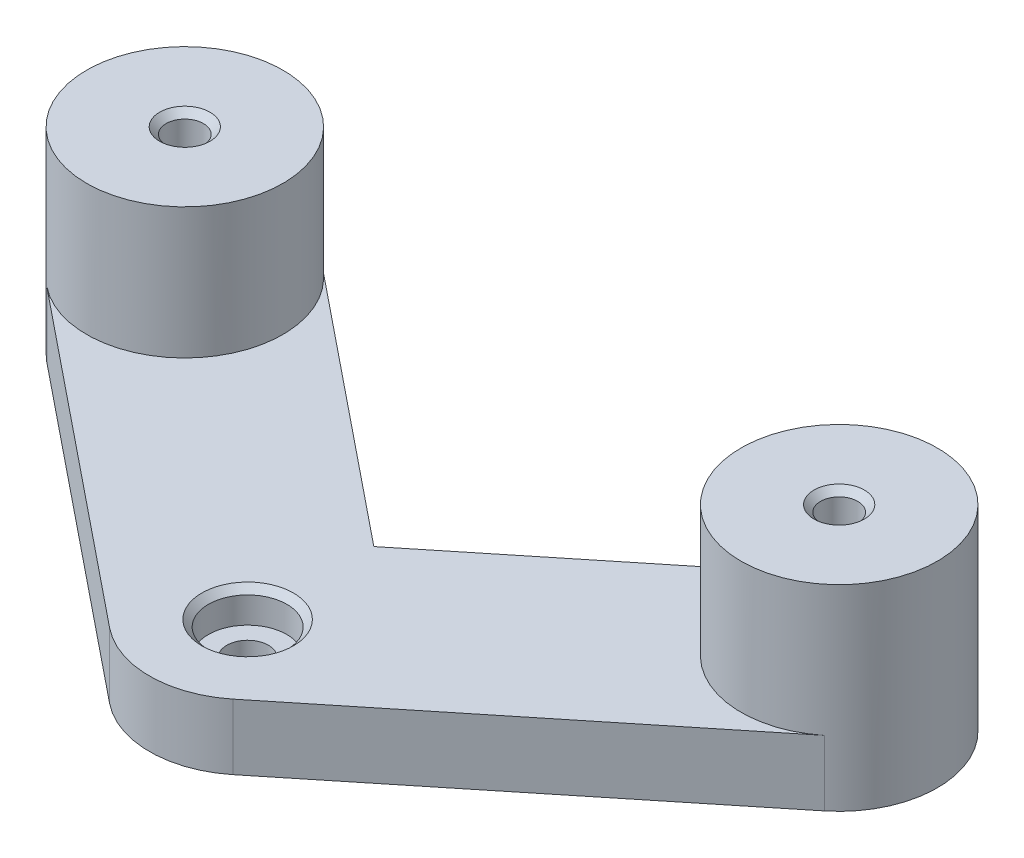
SolidWorks part; units mm, degrees
ref_plane "Front Plane" through (0, 0, 0) normal (0, 0, 1) x (1, 0, 0)
ref_plane "Top Plane" through (0, 0, 0) normal (0, 1, 0) x (1, 0, 0)
ref_plane "Right Plane" through (0, 0, 0) normal (1, 0, 0) x (0, 0, -1)
sketch "Sketch1" plane through (0, 0, 0) normal (0, 1, 0) x (1, 0, 0)
  circle A0 centre (0, 0) radius 100 construction
  circle A1 centre (-100, 0) radius 2.85
  circle A2 centre (-50, 86.6025) radius 2.85
  circle A3 centre (50, 86.6025) radius 2.85
  circle A4 centre (100, 0) radius 2.85
  circle A5 centre (50, -86.6025) radius 2.85
  circle A6 centre (-50, -86.6025) radius 2.85
  point P18 (0, 0)
  dimension "D1" = 200
  dimension "D2" = 5.7
  dimension "D3" = 6
sketch "Sketch3" plane through (0, 0, 0) normal (0, 1, 0) x (1, 0, 0)
  line L0 (-203.2, 152.4) -> (-203.2, -49.2102) construction
  line L1 (-203.2, 152.4) -> (37.0656, 152.4) construction
  circle A0 centre (-203.2, 152.4) radius 3.175
  circle A1 centre (-177.8, 152.4) radius 3.175
  circle A2 centre (-152.4, 152.4) radius 3.175
  circle A3 centre (-127, 152.4) radius 3.175
  circle A4 centre (-101.6, 152.4) radius 3.175
  circle A5 centre (-76.2, 152.4) radius 3.175
  circle A6 centre (-50.8, 152.4) radius 3.175
  circle A7 centre (-25.4, 152.4) radius 3.175
  circle A8 centre (0, 152.4) radius 3.175
  circle A9 centre (25.4, 152.4) radius 3.175
  circle A10 centre (50.8, 152.4) radius 3.175
  circle A11 centre (76.2, 152.4) radius 3.175
  circle A12 centre (101.6, 152.4) radius 3.175
  circle A13 centre (127, 152.4) radius 3.175
  circle A14 centre (152.4, 152.4) radius 3.175
  circle A15 centre (-177.8, 127) radius 3.175
  circle A16 centre (-152.4, 127) radius 3.175
  circle A17 centre (-127, 127) radius 3.175
  circle A18 centre (-101.6, 127) radius 3.175
  circle A19 centre (-76.2, 127) radius 3.175
  circle A20 centre (-50.8, 127) radius 3.175
  circle A21 centre (-25.4, 127) radius 3.175
  circle A22 centre (0, 127) radius 3.175
  circle A23 centre (25.4, 127) radius 3.175
  circle A24 centre (50.8, 127) radius 3.175
  circle A25 centre (76.2, 127) radius 3.175
  circle A26 centre (101.6, 127) radius 3.175
  circle A27 centre (127, 127) radius 3.175
  circle A28 centre (152.4, 127) radius 3.175
  circle A29 centre (-177.8, 101.6) radius 3.175
  circle A30 centre (-152.4, 101.6) radius 3.175
  circle A31 centre (-127, 101.6) radius 3.175
  circle A32 centre (-101.6, 101.6) radius 3.175
  circle A33 centre (-76.2, 101.6) radius 3.175
  circle A34 centre (-50.8, 101.6) radius 3.175
  circle A35 centre (-25.4, 101.6) radius 3.175
  circle A36 centre (0, 101.6) radius 3.175
  circle A37 centre (25.4, 101.6) radius 3.175
  circle A38 centre (50.8, 101.6) radius 3.175
  circle A39 centre (76.2, 101.6) radius 3.175
  circle A40 centre (101.6, 101.6) radius 3.175
  circle A41 centre (127, 101.6) radius 3.175
  circle A42 centre (152.4, 101.6) radius 3.175
  circle A43 centre (-177.8, 76.2) radius 3.175
  circle A44 centre (-152.4, 76.2) radius 3.175
  circle A45 centre (-127, 76.2) radius 3.175
  circle A46 centre (-101.6, 76.2) radius 3.175
  circle A47 centre (-76.2, 76.2) radius 3.175
  circle A48 centre (-50.8, 76.2) radius 3.175
  circle A49 centre (-25.4, 76.2) radius 3.175
  circle A50 centre (0, 76.2) radius 3.175
  circle A51 centre (25.4, 76.2) radius 3.175
  circle A52 centre (50.8, 76.2) radius 3.175
  circle A53 centre (76.2, 76.2) radius 3.175
  circle A54 centre (101.6, 76.2) radius 3.175
  circle A55 centre (127, 76.2) radius 3.175
  circle A56 centre (152.4, 76.2) radius 3.175
  circle A57 centre (-177.8, 50.8) radius 3.175
  circle A58 centre (-152.4, 50.8) radius 3.175
  circle A59 centre (-127, 50.8) radius 3.175
  circle A60 centre (-101.6, 50.8) radius 3.175
  circle A61 centre (-76.2, 50.8) radius 3.175
  circle A62 centre (-50.8, 50.8) radius 3.175
  circle A63 centre (-25.4, 50.8) radius 3.175
  circle A64 centre (0, 50.8) radius 3.175
  circle A65 centre (25.4, 50.8) radius 3.175
  circle A66 centre (50.8, 50.8) radius 3.175
  circle A67 centre (76.2, 50.8) radius 3.175
  circle A68 centre (101.6, 50.8) radius 3.175
  circle A69 centre (127, 50.8) radius 3.175
  circle A70 centre (152.4, 50.8) radius 3.175
  circle A71 centre (-177.8, 25.4) radius 3.175
  circle A72 centre (-152.4, 25.4) radius 3.175
  circle A73 centre (-127, 25.4) radius 3.175
  circle A74 centre (-101.6, 25.4) radius 3.175
  circle A75 centre (-76.2, 25.4) radius 3.175
  circle A76 centre (-50.8, 25.4) radius 3.175
  circle A77 centre (-25.4, 25.4) radius 3.175
  circle A78 centre (0, 25.4) radius 3.175
  circle A79 centre (25.4, 25.4) radius 3.175
  circle A80 centre (50.8, 25.4) radius 3.175
  circle A81 centre (76.2, 25.4) radius 3.175
  circle A82 centre (101.6, 25.4) radius 3.175
  circle A83 centre (127, 25.4) radius 3.175
  circle A84 centre (152.4, 25.4) radius 3.175
  circle A85 centre (-177.8, 0) radius 3.175
  circle A86 centre (-152.4, 0) radius 3.175
  circle A87 centre (-127, 0) radius 3.175
  circle A88 centre (-101.6, 0) radius 3.175
  circle A89 centre (-76.2, 0) radius 3.175
  circle A90 centre (-50.8, 0) radius 3.175
  circle A91 centre (-25.4, 0) radius 3.175
  circle A92 centre (0, 0) radius 3.175
  circle A93 centre (25.4, 0) radius 3.175
  circle A94 centre (50.8, 0) radius 3.175
  circle A95 centre (76.2, 0) radius 3.175
  circle A96 centre (101.6, 0) radius 3.175
  circle A97 centre (127, 0) radius 3.175
  circle A98 centre (152.4, 0) radius 3.175
  circle A99 centre (-177.8, -25.4) radius 3.175
  circle A100 centre (-152.4, -25.4) radius 3.175
  circle A101 centre (-127, -25.4) radius 3.175
  circle A102 centre (-101.6, -25.4) radius 3.175
  circle A103 centre (-76.2, -25.4) radius 3.175
  circle A104 centre (-50.8, -25.4) radius 3.175
  circle A105 centre (-25.4, -25.4) radius 3.175
  circle A106 centre (0, -25.4) radius 3.175
  circle A107 centre (25.4, -25.4) radius 3.175
  circle A108 centre (50.8, -25.4) radius 3.175
  circle A109 centre (76.2, -25.4) radius 3.175
  circle A110 centre (101.6, -25.4) radius 3.175
  circle A111 centre (127, -25.4) radius 3.175
  circle A112 centre (152.4, -25.4) radius 3.175
  circle A113 centre (-177.8, -50.8) radius 3.175
  circle A114 centre (-152.4, -50.8) radius 3.175
  circle A115 centre (-127, -50.8) radius 3.175
  circle A116 centre (-101.6, -50.8) radius 3.175
  circle A117 centre (-76.2, -50.8) radius 3.175
  circle A118 centre (-50.8, -50.8) radius 3.175
  circle A119 centre (-25.4, -50.8) radius 3.175
  circle A120 centre (0, -50.8) radius 3.175
  circle A121 centre (25.4, -50.8) radius 3.175
  circle A122 centre (50.8, -50.8) radius 3.175
  circle A123 centre (76.2, -50.8) radius 3.175
  circle A124 centre (101.6, -50.8) radius 3.175
  circle A125 centre (127, -50.8) radius 3.175
  circle A126 centre (152.4, -50.8) radius 3.175
  circle A127 centre (-177.8, -76.2) radius 3.175
  circle A128 centre (-152.4, -76.2) radius 3.175
  circle A129 centre (-127, -76.2) radius 3.175
  circle A130 centre (-101.6, -76.2) radius 3.175
  circle A131 centre (-76.2, -76.2) radius 3.175
  circle A132 centre (-50.8, -76.2) radius 3.175
  circle A133 centre (-25.4, -76.2) radius 3.175
  circle A134 centre (0, -76.2) radius 3.175
  circle A135 centre (25.4, -76.2) radius 3.175
  circle A136 centre (50.8, -76.2) radius 3.175
  circle A137 centre (76.2, -76.2) radius 3.175
  circle A138 centre (101.6, -76.2) radius 3.175
  circle A139 centre (127, -76.2) radius 3.175
  circle A140 centre (152.4, -76.2) radius 3.175
  circle A141 centre (-177.8, -101.6) radius 3.175
  circle A142 centre (-152.4, -101.6) radius 3.175
  circle A143 centre (-127, -101.6) radius 3.175
  circle A144 centre (-101.6, -101.6) radius 3.175
  circle A145 centre (-76.2, -101.6) radius 3.175
  circle A146 centre (-50.8, -101.6) radius 3.175
  circle A147 centre (-25.4, -101.6) radius 3.175
  circle A148 centre (0, -101.6) radius 3.175
  circle A149 centre (25.4, -101.6) radius 3.175
  circle A150 centre (50.8, -101.6) radius 3.175
  circle A151 centre (76.2, -101.6) radius 3.175
  circle A152 centre (101.6, -101.6) radius 3.175
  circle A153 centre (127, -101.6) radius 3.175
  circle A154 centre (152.4, -101.6) radius 3.175
  circle A155 centre (-177.8, -127) radius 3.175
  circle A156 centre (-152.4, -127) radius 3.175
  circle A157 centre (-127, -127) radius 3.175
  circle A158 centre (-101.6, -127) radius 3.175
  circle A159 centre (-76.2, -127) radius 3.175
  circle A160 centre (-50.8, -127) radius 3.175
  circle A161 centre (-25.4, -127) radius 3.175
  circle A162 centre (0, -127) radius 3.175
  circle A163 centre (25.4, -127) radius 3.175
  circle A164 centre (50.8, -127) radius 3.175
  circle A165 centre (76.2, -127) radius 3.175
  circle A166 centre (101.6, -127) radius 3.175
  circle A167 centre (127, -127) radius 3.175
  circle A168 centre (152.4, -127) radius 3.175
  circle A169 centre (-177.8, -152.4) radius 3.175
  circle A170 centre (-152.4, -152.4) radius 3.175
  circle A171 centre (-127, -152.4) radius 3.175
  circle A172 centre (-101.6, -152.4) radius 3.175
  circle A173 centre (-76.2, -152.4) radius 3.175
  circle A174 centre (-50.8, -152.4) radius 3.175
  circle A175 centre (-25.4, -152.4) radius 3.175
  circle A176 centre (0, -152.4) radius 3.175
  circle A177 centre (25.4, -152.4) radius 3.175
  circle A178 centre (50.8, -152.4) radius 3.175
  circle A179 centre (76.2, -152.4) radius 3.175
  circle A180 centre (101.6, -152.4) radius 3.175
  circle A181 centre (127, -152.4) radius 3.175
  circle A182 centre (152.4, -152.4) radius 3.175
  circle A183 centre (-177.8, -177.8) radius 3.175
  circle A184 centre (-152.4, -177.8) radius 3.175
  circle A185 centre (-127, -177.8) radius 3.175
  circle A186 centre (-101.6, -177.8) radius 3.175
  circle A187 centre (-76.2, -177.8) radius 3.175
  circle A188 centre (-50.8, -177.8) radius 3.175
  circle A189 centre (-25.4, -177.8) radius 3.175
  circle A190 centre (0, -177.8) radius 3.175
  circle A191 centre (25.4, -177.8) radius 3.175
  circle A192 centre (50.8, -177.8) radius 3.175
  circle A193 centre (76.2, -177.8) radius 3.175
  circle A194 centre (101.6, -177.8) radius 3.175
  circle A195 centre (127, -177.8) radius 3.175
  circle A196 centre (152.4, -177.8) radius 3.175
  circle A197 centre (-177.8, -203.2) radius 3.175
  circle A198 centre (-152.4, -203.2) radius 3.175
  circle A199 centre (-127, -203.2) radius 3.175
  circle A200 centre (-101.6, -203.2) radius 3.175
  circle A201 centre (-76.2, -203.2) radius 3.175
  circle A202 centre (-50.8, -203.2) radius 3.175
  circle A203 centre (-25.4, -203.2) radius 3.175
  circle A204 centre (0, -203.2) radius 3.175
  circle A205 centre (25.4, -203.2) radius 3.175
  circle A206 centre (50.8, -203.2) radius 3.175
  circle A207 centre (76.2, -203.2) radius 3.175
  circle A208 centre (101.6, -203.2) radius 3.175
  circle A209 centre (127, -203.2) radius 3.175
  circle A210 centre (152.4, -203.2) radius 3.175
  circle A211 centre (-203.2, 127) radius 3.175
  circle A212 centre (-203.2, 101.6) radius 3.175
  circle A213 centre (-203.2, 76.2) radius 3.175
  circle A214 centre (-203.2, 50.8) radius 3.175
  circle A215 centre (-203.2, 25.4) radius 3.175
  circle A216 centre (-203.2, 0) radius 3.175
  circle A217 centre (-203.2, -25.4) radius 3.175
  circle A218 centre (-203.2, -50.8) radius 3.175
  circle A219 centre (-203.2, -76.2) radius 3.175
  circle A220 centre (-203.2, -101.6) radius 3.175
  circle A221 centre (-203.2, -127) radius 3.175
  circle A222 centre (-203.2, -152.4) radius 3.175
  circle A223 centre (-203.2, -177.8) radius 3.175
  circle A224 centre (-203.2, -203.2) radius 3.175
  dimension "D1" = 6.35
  dimension "D3" = 15
  dimension "D2" = 15
sketch "Sketch10" plane through (0, 0, 0) normal (0, 1, 0) x (1, 0, 0)
  line L0 (-50, -86.6025) -> (0, -127) construction
  line L1 (-40.5731, -74.9349) -> (0, -107.7159)
  line L2 (-59.4269, -98.2702) -> (-9.4269, -138.6677)
  line L3 (0, -127) -> (50, -86.6025) construction
  line L4 (0, -107.7159) -> (40.5731, -74.9349)
  line L5 (9.4269, -138.6677) -> (59.4269, -98.2702)
  arc A0 (-40.5731, -74.9349) -> (-59.4269, -98.2702) centre (-50, -86.6025) ccw
  arc A2 (-9.4269, -138.6677) -> (9.4269, -138.6677) centre (0, -127) ccw
  arc A3 (59.4269, -98.2702) -> (40.5731, -74.9349) centre (50, -86.6025) ccw
  circle A8 centre (0, -127) radius 3.175
  circle A9 centre (0, -127) radius 3.175 construction
  point P4 (-25, -106.8013)
  point P9 (25, -106.8013)
  dimension "D1" = 15
  dimension "D2" = 15
extrude "Boss-Extrude4" add sketch "Sketch10" along normal blind 10 separate body
sketch "Sketch11" plane through (0, 10, 0) normal (0, 1, 0) x (1, 0, 0)
  circle A0 centre (-50, -86.6025) radius 15
  circle A1 centre (50, -86.6025) radius 15
extrude "Boss-Extrude5" add sketch "Sketch11" along normal blind 20
sketch "Sketch12" plane through (0, 30, 0) normal (0, 1, 0) x (1, 0, 0)
  circle A0 centre (-50, -86.6025) radius 2.85
  circle A1 centre (50, -86.6025) radius 2.85
extrude "Cut-Extrude4" cut sketch "Sketch12" against normal blind 37
sketch "Sketch13" plane through (0, 10, 0) normal (0, 1, 0) x (1, 0, 0)
  circle A0 centre (0, -127) radius 6
extrude "Cut-Extrude5" cut sketch "Sketch13" against normal blind 5
chamfer "Chamfer2" distance 1 angle 45 3 edges at (50, 30, 89.4525) (0, 10, 133) (-50, 30, 89.4525)
